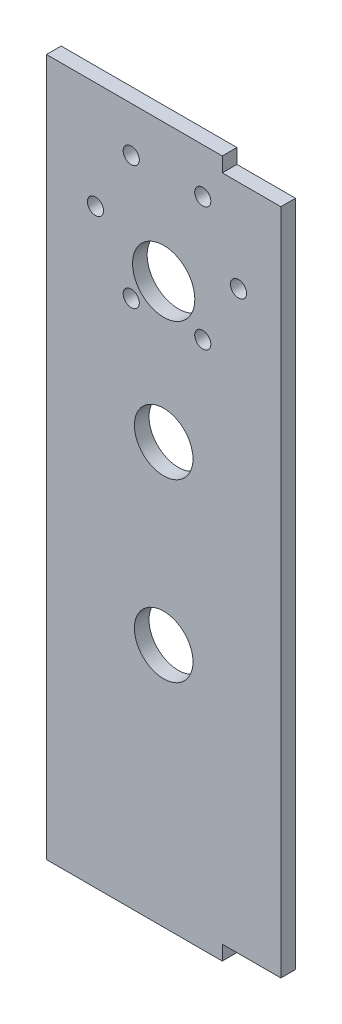
SolidWorks part; units mm, degrees
ref_plane "Спереди" through (0, 0, 0) normal (0, 0, 1) x (1, 0, 0)
ref_plane "Сверху" through (0, 0, 0) normal (0, 1, 0) x (1, 0, 0)
ref_plane "Справа" through (0, 0, 0) normal (1, 0, 0) x (0, 0, -1)
sketch "Эскиз1" plane through (0, 0, 0) normal (0, 0, 1) x (1, 0, 0)
  line L0 (6.35, 72.0308) -> (6.35, 151.13) construction
  line L1 (19.05, 151.13) -> (-19.05, 151.13)
  line L13 (19.05, 0) -> (-19.05, 0)
  line L15 (-19.05, 0) -> (-19.05, 151.13)
  line L16 (19.05, 0) -> (19.05, 3.175)
  line L17 (19.05, 3.175) -> (31.75, 3.175)
  line L18 (31.75, 3.175) -> (31.75, 147.955)
  line L19 (31.75, 147.955) -> (19.05, 147.955)
  line L20 (19.05, 147.955) -> (19.05, 151.13)
  line L21 (-19.05, 75.565) -> (31.75, 75.565) construction
  line L22 (6.35, 72.0308) -> (6.35, 107.9679) construction
  line L23 (22.5681, 127.955) -> (14.8181, 141.3784) construction
  line L24 (14.8181, 141.3784) -> (-0.6819, 141.3784) construction
  line L25 (-0.6819, 141.3784) -> (-8.4319, 127.955) construction
  line L26 (-8.4319, 127.955) -> (-0.6819, 114.5316) construction
  line L27 (-0.6819, 114.5316) -> (14.8181, 114.5316) construction
  line L28 (14.8181, 114.5316) -> (22.5681, 127.955) construction
  circle A0 centre (6.35, 52.9808) radius 19.05 construction
  circle A8 centre (6.35, 91.0808) radius 19.05 construction
  circle A9 centre (6.35, 121.2433) radius 6.75
  circle A10 centre (7.0681, 127.955) radius 13.4234 construction
  circle A12 centre (22.5681, 127.955) radius 1.75
  circle A13 centre (14.8181, 114.5316) radius 1.75
  circle A14 centre (-0.6819, 114.5316) radius 1.75
  circle A15 centre (-8.4319, 127.955) radius 1.75
  circle A16 centre (-0.6819, 141.3784) radius 1.75
  circle A17 centre (14.8181, 141.3784) radius 1.75
  circle A19 centre (7.0681, 127.955) radius 20 construction
  circle A20 centre (6.35, 121.2433) radius 11.1125 construction
  circle A21 centre (6.35, 91.0808) radius 6.35
  circle A22 centre (6.35, 52.9808) radius 6.35
  point P22 (31.75, 75.565)
  point P23 (-19.05, 75.565)
  point P31 (0, 0)
  point P39 (7.0681, 114.5316)
  point P41 (0, 0)
  point P42 (0, 0)
  dimension "D6" = 13.5
  dimension "D8" = 40
  dimension "D9" = 35.9371
  dimension "D5" = 3.5
  dimension "D10" = 22.225
  dimension "D11" = 12.7
  dimension "D12" = 12.7
  dimension "D13" = 38.1
  dimension "D14" = 52.9808
  dimension "D1" = 38.1
  dimension "D2" = 50.8
  dimension "D3" = 15.5
  dimension "D4" = 144.78
  dimension "D7" = 151.13
  dimension "D15" = 25.4
extrude "Бобышка-Вытянуть1" add sketch "Эскиз1" along normal blind 3.175
